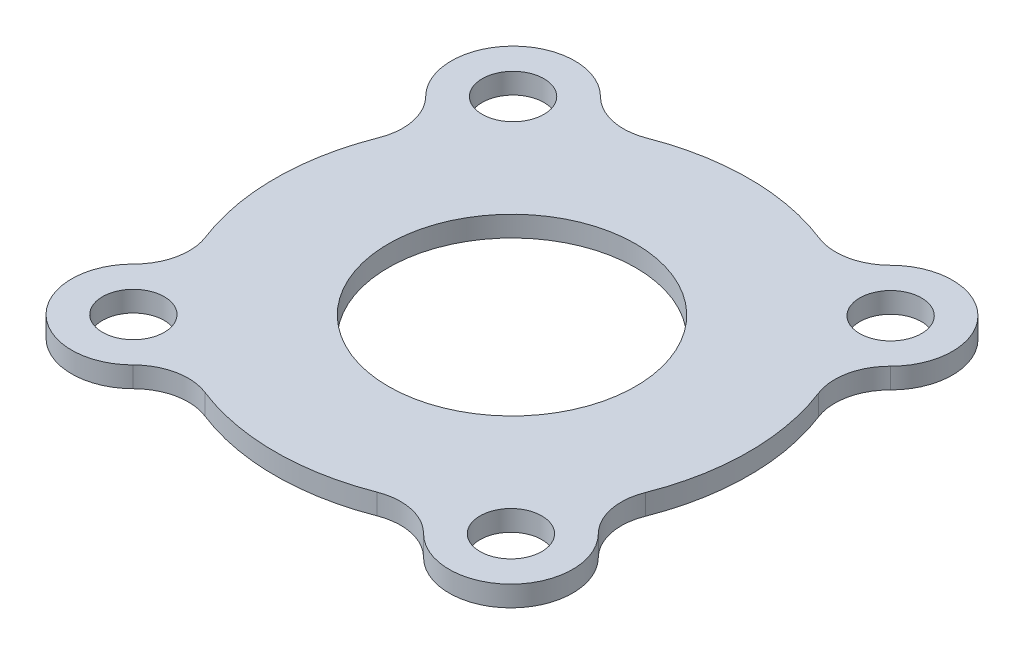
SolidWorks part; units mm, degrees
ref_plane "Front Plane" through (0, 0, 0) normal (0, 0, 1) x (1, 0, 0)
ref_plane "Top Plane" through (0, 0, 0) normal (0, 1, 0) x (1, 0, 0)
ref_plane "Right Plane" through (0, 0, 0) normal (1, 0, 0) x (0, 0, -1)
sketch "Sketch1" plane through (0, 0, 0) normal (0, 1, 0) x (1, 0, 0)
  circle A4 centre (0, 0) radius 8
  line B0 (0, 0) -> (-39.9998, 0.1142) construction
  line B1 (-0.0262, -9.1924) -> (0, 0) construction
  line B2 (-0.0262, -9.1924) -> (0, 0) construction
  line B3 (0, 0) -> (9.1661, -9.2186) construction
  line B4 (9.1661, -9.2186) -> (-40.1666, -58.2703) construction
  circle B5 centre (0, 0) radius 6
  circle B6 centre (0, 0) radius 9.5
  circle B7 centre (0, 0) radius 11.5
  circle B8 centre (9.1661, -9.2186) radius 1.5
  arc B9 (9.6484, -6.2576) -> (6.2024, -9.684) centre (9.1661, -9.2186) cw
  arc B10 (10.6983, -4.2186) -> (11.2935, -7.1033) centre (13.2018, -5.2058) ccw
  arc B11 (4.1574, -10.7222) -> (7.0387, -11.3339) centre (5.1304, -13.2314) cw
  arc B12 (-10.7222, -4.1574) -> (-11.3339, -7.0387) centre (-13.2314, -5.1304) cw
  arc B13 (-4.2186, -10.6983) -> (-7.1033, -11.2935) centre (-5.2058, -13.2018) ccw
  arc B14 (-4.1574, 10.7222) -> (-7.0387, 11.3339) centre (-5.1304, 13.2314) cw
  arc B15 (-10.6983, 4.2186) -> (-11.2935, 7.1033) centre (-13.2018, 5.2058) ccw
  arc B16 (10.7222, 4.1574) -> (11.3339, 7.0387) centre (13.2314, 5.1304) cw
  arc B17 (4.2186, 10.6983) -> (7.1033, 11.2935) centre (5.2058, 13.2018) ccw
  arc B18 (-6.2576, -9.6484) -> (-9.684, -6.2024) centre (-9.2186, -9.1661) cw
  circle B19 centre (-9.2186, -9.1661) radius 1.5
  arc B20 (-9.6484, 6.2576) -> (-6.2024, 9.684) centre (-9.1661, 9.2186) cw
  circle B21 centre (-9.1661, 9.2186) radius 1.5
  arc B22 (6.2576, 9.6484) -> (9.684, 6.2024) centre (9.2186, 9.1661) cw
  circle B23 centre (9.2186, 9.1661) radius 1.5
  dimension "D1" = 1.5
sketch_block_instance "Block1-1"
sketch_block "Block1" parameters "D1"=19, "D2"=12, "D4"=3, "D3"=2, "D6"=13, "D7"=4.5, "D8"=90, "D5"=45
extrude "Boss-Extrude1" add sketch "Sketch1" along normal blind 1 contours B9 B7 B8 | B10 B7 B9 | B7 B11 B9 | B7 B6 | B7 B19 B18 | B7 B18 B13 | B12 B18 B7 | B7 B23 B22 | B7 B22 B17 | B16 B22 B7 | B7 B21 B20 | B14 B20 B7 | B7 B20 B15 | B6 A4 | A4 B5
sketch "Sketch3" plane through (0, 0, 0) normal (0, 1, 0) x (1, 0, 0)
  circle A0 centre (0, 0) radius 9.5
  circle A1 centre (0, 0) radius 8
  dimension "D1" = 1.5
  dimension "D2" = 19
extrude "Boss-Extrude2" add sketch "Sketch3" against normal blind 1
